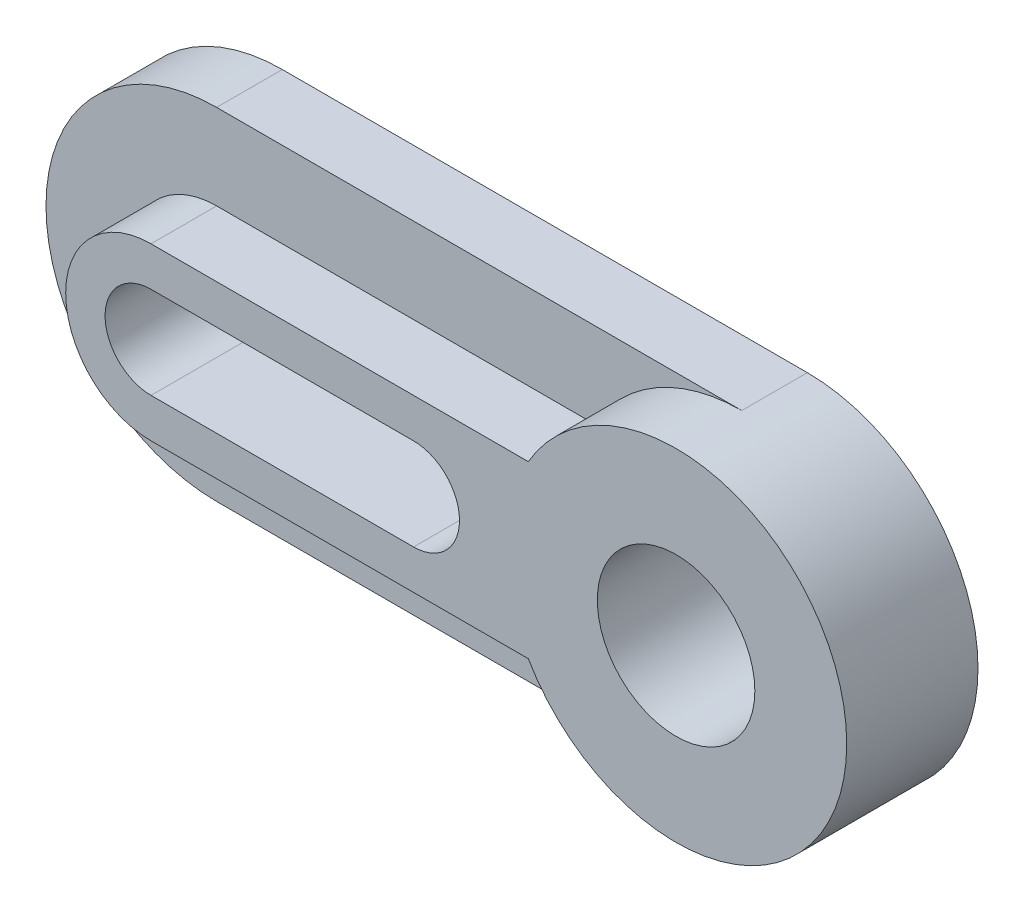
SolidWorks part; units mm, degrees
material "Ferro fundido maleável"
ref_plane "Plano frontal" through (0, 0, 0) normal (0, 0, 1) x (1, 0, 0)
ref_plane "Plano superior" through (0, 0, 0) normal (0, 1, 0) x (1, 0, 0)
ref_plane "Plano direito" through (0, 0, 0) normal (1, 0, 0) x (0, 0, -1)
sketch "Esboço1" plane through (0, 0, 0) normal (0, 0, 1) x (1, 0, 0)
  line L0 (0, 0) -> (80, 0) construction
  line L1 (0, 26) -> (80, 26)
  line L2 (0, -26) -> (80, -26)
  arc A0 (0, 26) -> (0, -26) centre (0, 0) ccw
  arc A1 (80, -26) -> (80, 26) centre (80, 0) ccw
  point P3 (40, 0)
  dimension "D2" = 26
  dimension "D1" = 80
extrude "Ressalto-extrusão1" add sketch "Esboço1" along normal blind 10
sketch "Esboço2" plane through (0, 0, 10) normal (0, 0, 1) x (1, 0, 0)
  line L0 (0, 13) -> (57.4833, 13)
  line L1 (0, -13) -> (57.4833, -13)
  arc A0 (0, 13) -> (0, -13) centre (0, 0) ccw
  arc A1 (57.4833, -13) -> (57.4833, 13) centre (80, 0) ccw
  arc A2 (80, -26) -> (80, 26) centre (80, 0) ccw construction
  dimension "D1" = 26
extrude "Ressalto-extrusão2" add sketch "Esboço2" along normal blind 10
sketch "Esboço3" plane through (0, 0, 20) normal (0, 0, 1) x (1, 0, 0)
  line L0 (0, 0) -> (40, 0) construction
  line L1 (0, 7) -> (40, 7)
  line L2 (0, -7) -> (40, -7)
  arc A0 (0, 7) -> (0, -7) centre (0, 0) ccw
  arc A1 (40, -7) -> (40, 7) centre (40, 0) ccw
  circle A2 centre (80, 0) radius 12
  point P3 (20, 0)
  dimension "D1" = 7
  dimension "D3" = 24
  dimension "D2" = 40
extrude "Corte-extrusão1" cut sketch "Esboço3" against normal through all
